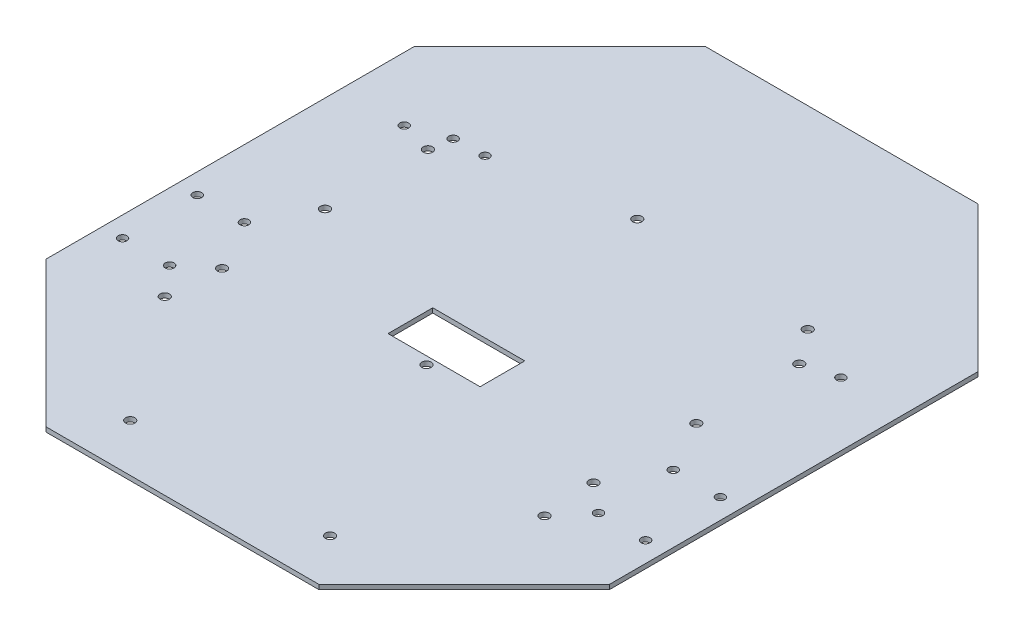
SolidWorks part; units mm, degrees
ref_plane "Front Plane" through (0, 0, 0) normal (0, 0, 1) x (1, 0, 0)
ref_plane "Top Plane" through (0, 0, 0) normal (0, 1, 0) x (1, 0, 0)
ref_plane "Right Plane" through (0, 0, 0) normal (1, 0, 0) x (0, 0, -1)
sketch "Sketch14" plane through (0, 0, 0) normal (0, 1, 0) x (1, 0, 0)
  line L1 (224, 92.7838) -> (92.7838, 224)
  line L2 (92.7838, 224) -> (-92.7838, 224)
  line L3 (-92.7838, 224) -> (-224, 92.7838)
  line L4 (-224, 92.7838) -> (-224, -92.7838)
  line L5 (-224, -92.7838) -> (-92.7838, -224)
  line L6 (-92.7838, -224) -> (92.7838, -224)
  line L7 (92.7838, -224) -> (224, -92.7838)
  line L8 (224, -92.7838) -> (224, 92.7838)
  circle A0 centre (0, 0) radius 224 construction
extrude "Boss-Extrude2" add sketch "Sketch14" along normal blind 3.12
sketch "Sketch16" plane through (0, 0, 0) normal (0, -1, 0) x (1, 0, 0)
  line L0 (-191.5, -224) -> (-191.5, 224)
  line L1 (-191.5, -224) -> (191.5, -224)
  line L2 (-191.5, 224) -> (191.5, 224)
  line L3 (191.5, -224) -> (191.5, 224)
  line L4 (-191.5, -224) -> (191.5, 224) construction
  line L5 (-191.5, 224) -> (191.5, -224) construction
  point P1 (0, 0)
  dimension "D1" = 383
ref_point "Point9"
ref_point "Point10"
sketch "Sketch17" plane through (0, 0, 0) normal (0, -1, 0) x (1, 0, 0)
  line L0 (191.5, 125.2838) -> (191.5, -125.742)
  line L1 (191.5, -125.742) -> (224, -92.7838)
  line L2 (224, -92.7838) -> (224, 92.7838)
  line L3 (224, 92.7838) -> (191.5, 125.2838)
extrude "Cut-Extrude2" cut sketch "Sketch17" against normal blind 4.12
ref_point "Point11"
ref_point "Point12"
sketch "Sketch18" plane through (0, 0, 0) normal (0, -1, 0) x (1, 0, 0)
  line L0 (-191.5, 125.2838) -> (-224, 92.7838)
  line L1 (-224, 92.7838) -> (-224, -92.7838)
  line L2 (-224, -92.7838) -> (-191.5, -125.2838)
  line L3 (-191.5, -125.2838) -> (-191.5, 125.2838)
extrude "Cut-Extrude3" cut sketch "Sketch18" against normal blind 4.12
hole_wizard "1/4 (0.25) Diameter Hole1" positions "Sketch19" profile "Sketch21" hole size "1/4" standard "ANSI Inch" end condition up to next
sketch "Sketch19" plane through (0, 3.12, 0) normal (0, 1, 0) x (1, 0, 0)
  point P2 (67.9635, -191.609)
  point P5 (-67.9265, -191.609)
  point P8 (-129.0643, -106.9889)
  point P11 (-126.1941, -70.8955)
  point P14 (-126.1941, -0.9185)
  point P17 (-126.1941, 69.0585)
  point P20 (-14.1039, 99.2591)
  point P23 (108.7305, 92.2995)
  point P26 (126.2311, 69.0585)
  point P29 (126.2311, -0.9185)
  point P32 (129.1013, -106.9889)
  point P35 (126.2311, -70.8955)
  point P38 (0.0185, -58.1955)
sketch "Sketch21" plane through (67.9635, 3.12, 191.609) normal (1, 0, 0) x (0, 0, 1)
  line L0 (0, 0) -> (0, 3.12)
  line L1 (0, 3.12) -> (3.175, 3.12)
  line L2 (3.175, 3.12) -> (3.175, 0)
  line L5 (3.175, 0) -> (0, 0)
  line L11 (0, -6.35) -> (0, 107.95) construction
  dimension "Thru Hole Dia." = 6.35
  dimension "Thru Hole Depth" = 3.12
sketch "Sketch22" plane through (0, 3.12, 0) normal (0, 1, 0) x (1, 0, 0)
  line L1 (31.1658, -52.8764) -> (-31.3997, -52.8764)
  line L2 (31.1658, -52.8764) -> (31.1658, -22.4822)
  line L3 (31.1658, -22.4822) -> (-31.3997, -22.4822)
  line L4 (-31.3997, -52.8764) -> (-31.3997, -22.4822)
extrude "Cut-Extrude4" cut sketch "Sketch22" against normal up to next
sketch "Sketch23" plane through (0, 0, 224) normal (0, 0, 1) x (1, 0, 0)
  line L0 (0, 3.12) -> (0, 0)
  line L1 (-92.7838, 3.12) -> (92.7838, 3.12) construction
  line L2 (-92.7838, 0) -> (92.7838, 0) construction
hole_wizard "Ø6.0mm Dowel Hole2" positions "Sketch24" profile "Sketch25" hole size "Ø6.0" standard "ANSI Metric" end condition up to next
sketch "Sketch24" plane through (0, 3.12, 0) normal (0, 1, 0) x (1, 0, 0)
  point P0 (-177.7815, -36.1589)
  point P3 (-177.7815, -86.9889)
  point P6 (-145.7415, -36.1589)
  point P9 (-145.7415, -86.9889)
  point P12 (145.7785, -86.9889)
  point P15 (177.8185, -86.9889)
  point P18 (177.8185, -36.1589)
  point P21 (145.7785, -36.1589)
sketch "Sketch25" plane through (-177.7815, 3.12, 36.1589) normal (1, 0, 0) x (0, 0, 1)
  line L0 (0, 0) -> (0, 3.12)
  line L1 (0, 3.12) -> (3, 3.12)
  line L2 (3, 3.12) -> (3, 0)
  line L5 (3, 0) -> (0, 0)
  line L11 (0, -6.35) -> (0, 107.95) construction
  dimension "Thru Hole Dia." = 6
  dimension "Thru Hole Depth" = 3.12
hole_wizard "Ø6.0mm Dowel Hole1" positions "Sketch26" profile "Sketch27" hole size "Ø6.0" standard "ANSI Metric" end condition up to next
sketch "Sketch26" plane through (0, 3.12, 0) normal (0, 1, 0) x (1, 0, 0)
  point P0 (-103.1515, 84.8073)
  point P3 (-124.0015, 84.0036)
sketch "Sketch27" plane through (-103.1515, 3.12, -84.8073) normal (1, 0, 0) x (0, 0, 1)
  line L0 (0, 0) -> (0, 3.12)
  line L1 (0, 3.12) -> (3, 3.12)
  line L2 (3, 3.12) -> (3, 0)
  line L5 (3, 0) -> (0, 0)
  line L11 (0, -6.35) -> (0, 107.95) construction
  dimension "Thru Hole Dia." = 6
  dimension "Thru Hole Depth" = 3.12
hole_wizard "Ø6.0mm Dowel Hole3" positions "Sketch28" profile "Sketch29" hole size "Ø6.0" standard "ANSI Metric" end condition up to next
sketch "Sketch28" plane through (0, 3.12, 0) normal (0, 1, 0) x (1, 0, 0)
  point P0 (-148.3962, 75.1271)
  point P2 (148.4173, 75.1508)
sketch "Sketch29" plane through (-148.3962, 3.12, -75.1271) normal (1, 0, 0) x (0, 0, 1)
  line L0 (0, 0) -> (0, 3.12)
  line L1 (0, 3.12) -> (3, 3.12)
  line L2 (3, 3.12) -> (3, 0)
  line L5 (3, 0) -> (0, 0)
  line L11 (0, -6.35) -> (0, 107.95) construction
  dimension "Thru Hole Dia." = 6
  dimension "Thru Hole Depth" = 3.12
